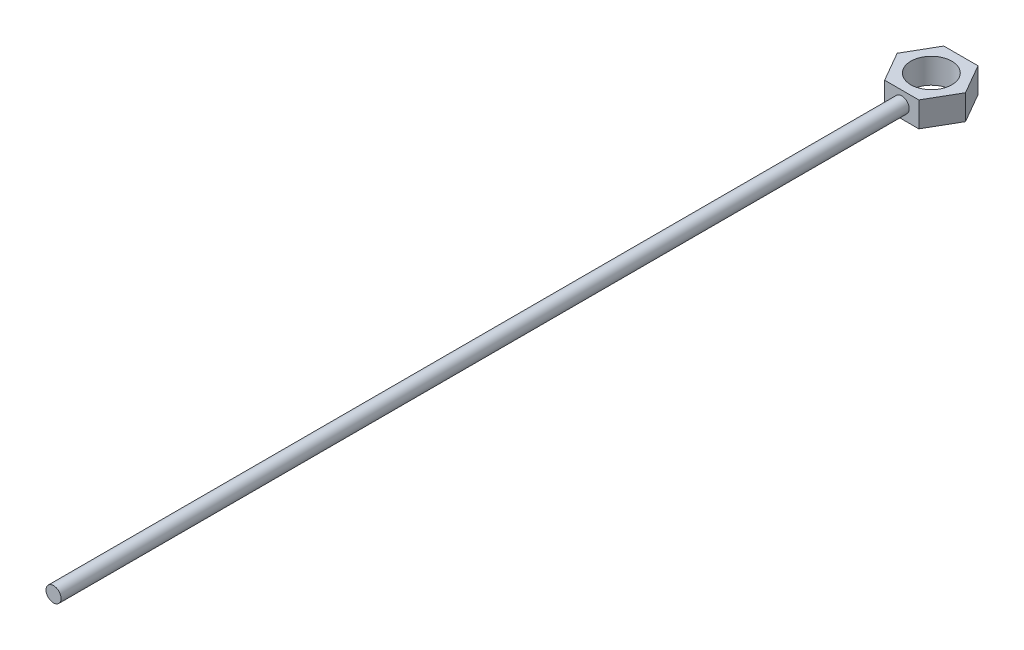
SolidWorks part; units mm, degrees
ref_plane "Alzado" through (0, 0, 0) normal (0, 0, 1) x (1, 0, 0)
ref_plane "Planta" through (0, 0, 0) normal (0, 1, 0) x (1, 0, 0)
ref_plane "Vista lateral" through (0, 0, 0) normal (1, 0, 0) x (0, 0, -1)
sketch "Croquis1" plane through (0, 0, 0) normal (0, 1, 0) x (1, 0, 0)
  line L1 (6.9213, 0) -> (3.4607, 5.994)
  line L2 (3.4607, 5.994) -> (-3.4607, 5.994)
  line L3 (-3.4607, 5.994) -> (-6.9213, 0)
  line L4 (-6.9213, 0) -> (-3.4607, -5.994)
  line L5 (-3.4607, -5.994) -> (3.4607, -5.994)
  line L6 (3.4607, -5.994) -> (6.9213, 0)
  circle A0 centre (0, 0) radius 3.9726
  circle A1 centre (0, 0) radius 5.994 construction
  dimension "D1" = 7.9451
extrude "Saliente-Extruir2" add sketch "Croquis1" along normal blind 5.08
sketch "Croquis2" plane through (0, 0, 0) normal (0, 0, 1) x (1, 0, 0)
  circle A0 centre (0, 2.54) radius 1.524
  dimension "D1" = 3.048
extrude "Saliente-Extruir4" add sketch "Croquis2" against normal blind 2.54 and the other way blind 177.8
sketch "Croquis3" plane through (0, 0, 0) normal (0, 1, 0) x (1, 0, 0)
  circle A0 centre (0, 0) radius 4.1497
extrude "Cortar-Extruir1" cut sketch "Croquis3" along normal blind 20.32 and the other way blind 21.336
